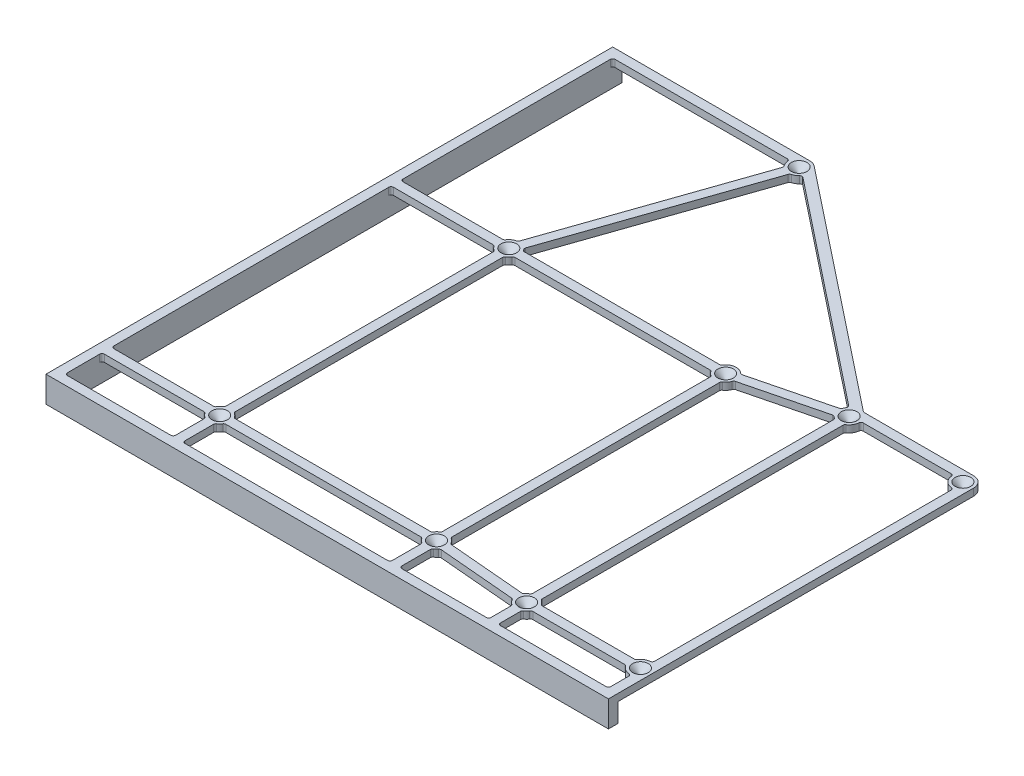
SolidWorks part; units mm, degrees
ref_plane "Front Plane" through (0, 0, 0) normal (0, 0, 1) x (1, 0, 0)
ref_plane "Top Plane" through (0, 0, 0) normal (0, 1, 0) x (1, 0, 0)
ref_plane "Right Plane" through (0, 0, 0) normal (1, 0, 0) x (0, 0, -1)
sketch "Sketch1" plane through (0, 0, 0) normal (0, 1, 0) x (1, 0, 0)
  line L0 (0, 0) -> (0, 15.62)
  line L1 (0, 234.9689) -> (-4, 234.9689)
  line L2 (-4, 234.9689) -> (-4, -4)
  line L3 (-4, -4) -> (233.18, -4)
  line L4 (233.18, -4) -> (233.18, 0)
  line L5 (229.18, 0) -> (182.68, 0)
  line L6 (180.68, 150) -> (228.68, 150) construction
  line L7 (47.62, 139.54) -> (139.06, 139.54) construction
  line L8 (47.62, 139.54) -> (47.62, 17.62) construction
  line L9 (47.62, 17.62) -> (139.06, 17.62) construction
  line L10 (139.06, 139.54) -> (139.06, 17.62) construction
  line L11 (146.68, 10) -> (40, 10) construction
  line L12 (146.68, 10) -> (146.68, 147.16) construction
  line L13 (146.68, 147.16) -> (40, 147.16) construction
  line L14 (40, 10) -> (40, 147.16) construction
  line L15 (180.68, 150) -> (180.68, 14) construction
  line L16 (180.68, 14) -> (228.68, 14) construction
  line L17 (228.68, 150) -> (228.68, 14) construction
  line L18 (232.68, 10) -> (176.68, 10) construction
  line L19 (232.68, 10) -> (232.68, 154) construction
  line L20 (232.68, 154) -> (176.68, 154) construction
  line L21 (176.68, 10) -> (176.68, 154) construction
  line L22 (229.18, 14) -> (233.18, 14) construction
  line L23 (233.18, 0) -> (233.18, 150)
  line L24 (229.18, 9.5279) -> (229.18, 0)
  line L25 (229.18, 18.4721) -> (229.18, 145.5279)
  line L26 (0, 234.9689) -> (79.1338, 234.9689)
  line L27 (228.68, 154.5) -> (182.2468, 154.5)
  line L28 (182.2468, 154.5) -> (81.9286, 233.9957)
  line L29 (178.68, 145.9689) -> (178.68, 18.0311)
  line L30 (185.1521, 150.5) -> (224.2079, 150.5)
  line L31 (184.7111, 16) -> (224.6489, 16)
  line L32 (184.7111, 12) -> (224.6489, 12)
  line L33 (224.6489, 16) -> (224.6489, 12) construction
  line L34 (224.6489, 16) -> (228.2321, 14.2222) construction
  line L35 (177.4855, 153.1694) -> (82.9494, 228.0832)
  line L36 (79.1338, 230.4689) -> (180.68, 150) construction
  line L37 (182.68, 145.9689) -> (182.68, 18.0311)
  line L38 (182.68, 9.9689) -> (182.68, 0)
  line L39 (178.68, 9.9689) -> (178.68, 0)
  line L40 (178.68, 18.0311) -> (182.68, 18.0311) construction
  line L41 (139.06, 17.62) -> (180.68, 14) construction
  line L42 (224.2079, 150.5) -> (224.2079, 154.5) construction
  line L43 (180.68, 150) -> (139.06, 139.54) construction
  line L44 (142.4821, 142.4622) -> (176.283, 150.9571)
  line L45 (141.06, 13.5889) -> (141.06, 0)
  line L46 (142.9027, 15.2782) -> (176.4907, 12.3568)
  line L47 (143.2493, 19.2632) -> (176.8373, 16.3418)
  line L48 (176.8373, 16.3418) -> (176.4907, 12.3568) construction
  line L49 (141.06, 21.6511) -> (141.06, 135.5089)
  line L50 (143.457, 138.5829) -> (177.2579, 147.0778)
  line L51 (176.283, 150.9571) -> (177.2579, 147.0778) construction
  line L52 (177.4855, 153.1694) -> (179.9698, 156.3044) construction
  line L53 (74.6616, 230.9689) -> (0, 230.9689)
  line L54 (74.6616, 230.9689) -> (74.6616, 234.9689) construction
  line L55 (45.62, 13.5889) -> (45.62, 0)
  line L56 (43.5889, 15.62) -> (0, 15.62)
  line L57 (51.6511, 15.62) -> (135.0289, 15.62)
  line L58 (49.62, 13.5889) -> (49.62, 0)
  line L59 (137.06, 13.5889) -> (137.06, 0)
  line L60 (51.6511, 19.62) -> (135.0289, 19.62)
  line L61 (137.06, 21.6511) -> (137.06, 135.5089)
  line L62 (75.924, 227.3149) -> (47.0503, 144.0038)
  line L63 (51.6511, 141.54) -> (135.0289, 141.54)
  line L64 (47.62, 139.54) -> (79.1338, 230.4689) construction
  line L65 (79.7034, 226.0051) -> (50.8298, 142.6939)
  line L66 (43.5889, 141.54) -> (0, 141.54)
  line L67 (43.5889, 137.54) -> (0, 137.54)
  line L68 (51.6511, 137.54) -> (135.0289, 137.54)
  line L69 (135.0289, 19.62) -> (135.0289, 15.62) construction
  line L70 (137.06, 13.5889) -> (141.06, 13.5889) construction
  line L71 (137.06, 21.6511) -> (141.06, 21.6511) construction
  line L72 (43.5889, 19.62) -> (0, 19.62)
  line L73 (45.62, 13.5889) -> (49.62, 13.5889) construction
  line L74 (45.62, 135.5089) -> (45.62, 21.6511)
  line L75 (49.62, 135.5089) -> (49.62, 21.6511)
  line L76 (135.0289, 137.54) -> (135.0289, 141.54) construction
  line L77 (47.0503, 144.0038) -> (50.8298, 142.6939) construction
  line L78 (0, 141.54) -> (0, 230.9689)
  line L79 (0, 19.62) -> (0, 137.54)
  line L80 (45.62, 0) -> (0, 0)
  line L81 (137.06, 0) -> (49.62, 0)
  line L82 (178.68, 0) -> (141.06, 0)
  circle A0 centre (47.62, 139.54) radius 7.62 construction
  circle A1 centre (139.06, 17.62) radius 7.62 construction
  circle A2 centre (47.62, 139.54) radius 0.5
  circle A3 centre (139.06, 139.54) radius 0.5
  circle A4 centre (139.06, 17.62) radius 0.5
  circle A5 centre (47.62, 17.62) radius 0.5
  circle A6 centre (180.68, 150) radius 4 construction
  circle A7 centre (228.68, 14) radius 4 construction
  circle A8 centre (180.68, 150) radius 0.5
  circle A9 centre (228.68, 150) radius 0.5
  circle A10 centre (228.68, 14) radius 0.5
  circle A11 centre (180.68, 14) radius 0.5
  arc A12 (229.18, 9.5279) -> (224.6489, 12) centre (228.68, 14) cw
  circle A13 centre (79.1338, 230.4689) radius 0.5
  arc A14 (233.18, 150) -> (228.68, 154.5) centre (228.68, 150) ccw
  arc A15 (79.1338, 234.9689) -> (81.9286, 233.9957) centre (79.1338, 230.4689) cw
  arc A16 (229.18, 18.4721) -> (224.6489, 16) centre (228.68, 14) ccw
  arc A17 (229.18, 145.5279) -> (224.2079, 150.5) centre (228.68, 150) cw
  arc A18 (185.1521, 150.5) -> (182.68, 145.9689) centre (180.68, 150) cw
  arc A19 (178.68, 9.9689) -> (176.4907, 12.3568) centre (180.68, 14) cw
  arc A20 (178.68, 18.0311) -> (176.8373, 16.3418) centre (180.68, 14) ccw
  arc A21 (182.68, 9.9689) -> (184.7111, 12) centre (180.68, 14) ccw
  arc A22 (184.7111, 16) -> (182.68, 18.0311) centre (180.68, 14) ccw
  arc A23 (177.4855, 153.1694) -> (176.283, 150.9571) centre (180.68, 150) ccw
  arc A24 (178.68, 145.9689) -> (177.2579, 147.0778) centre (180.68, 150) cw
  arc A25 (75.924, 227.3149) -> (74.6616, 230.9689) centre (79.1338, 230.4689) cw
  arc A26 (143.457, 138.5829) -> (141.06, 135.5089) centre (139.06, 139.54) cw
  arc A27 (143.2493, 19.2632) -> (141.06, 21.6511) centre (139.06, 17.62) ccw
  arc A28 (142.9027, 15.2782) -> (141.06, 13.5889) centre (139.06, 17.62) cw
  arc A29 (82.9494, 228.0832) -> (79.7034, 226.0051) centre (79.1338, 230.4689) cw
  arc A30 (137.06, 21.6511) -> (135.0289, 19.62) centre (139.06, 17.62) ccw
  arc A31 (137.06, 13.5889) -> (135.0289, 15.62) centre (139.06, 17.62) cw
  arc A32 (45.62, 13.5889) -> (43.5889, 15.62) centre (47.62, 17.62) cw
  arc A33 (43.5889, 19.62) -> (45.62, 21.6511) centre (47.62, 17.62) cw
  arc A34 (51.6511, 19.62) -> (49.62, 21.6511) centre (47.62, 17.62) ccw
  arc A35 (51.6511, 15.62) -> (49.62, 13.5889) centre (47.62, 17.62) cw
  arc A36 (137.06, 135.5089) -> (135.0289, 137.54) centre (139.06, 139.54) cw
  arc A37 (142.4821, 142.4622) -> (135.0289, 141.54) centre (139.06, 139.54) ccw
  arc A38 (51.6511, 137.54) -> (49.62, 135.5089) centre (47.62, 139.54) cw
  arc A39 (45.62, 135.5089) -> (43.5889, 137.54) centre (47.62, 139.54) cw
  arc A40 (43.5889, 141.54) -> (47.0503, 144.0038) centre (47.62, 139.54) cw
  arc A41 (50.8298, 142.6939) -> (51.6511, 141.54) centre (47.62, 139.54) cw
  point P101 (0, 0)
  dimension "D4" = 106.68
  dimension "D5" = 1
  dimension "D8" = 108.9
  dimension "D13" = 96.235
  dimension "D1" = 4
  dimension "D2" = 121.92
  dimension "D3" = 91.44
  dimension "D6" = 40
  dimension "D7" = 10
  dimension "D9" = 48
  dimension "D10" = 136
  dimension "D11" = 56
  dimension "D12" = 30
extrude "Boss-Extrude1" add sketch "Sketch1" along normal blind 3
sketch "Sketch2" plane through (0, 0, 0) normal (0, -1, 0) x (1, 0, 0)
  line L0 (-4, 4) -> (-4, -234.9689)
  line L1 (-4, -234.9689) -> (-4, 4) construction
  line L2 (-4, -234.9689) -> (0, -234.9689)
  line L3 (79.1338, -234.9689) -> (-4, -234.9689) construction
  line L4 (0, -234.9689) -> (0, 0)
  line L5 (0, 0) -> (233.18, 0)
  line L6 (233.18, 4) -> (233.18, -150) construction
  line L7 (233.18, 0) -> (233.18, 4)
  line L8 (233.18, 4) -> (-4, 4)
  point P13 (-4, -248.5482)
extrude "Boss-Extrude2" add sketch "Sketch2" along normal blind 8
chamfer "Chamfer1" distance 2.8 angle 45 9 edges at (47.62, 3, -17.12) (139.06, 3, -17.12) (180.68, 3, -13.5) (228.68, 3, -13.5) (228.68, 3, -149.5) (180.68, 3, -149.5) (139.06, 3, -139.04) (79.1338, 3, -229.9689) (47.62, 3, -139.04)
fillet "Fillet1" radius 1 68 edges at (182.2468, 1.5, -154.5) (176.8373, 1.5, -16.3418) (178.68, 1.5, -18.0311) (49.62, 1.5, 0) (0, -2.5, 0) (45.62, 1.5, 0) (45.62, 1.5, -13.5889) (43.5889, 1.5, -15.62) (43.5889, 1.5, -19.62) (45.62, 1.5, -21.6511) (49.62, 1.5, -21.6511) (51.6511, 1.5, -19.62) (49.62, 1.5, -13.5889) (51.6511, 1.5, -15.62) (0, 1.5, -15.62) (0, 1.5, -19.62) (0, 1.5, -137.54) (0, 1.5, -141.54) (43.5889, 1.5, -141.54) (47.0503, 1.5, -144.0038) (43.5889, 1.5, -137.54) (45.62, 1.5, -135.5089) (49.62, 1.5, -135.5089) (51.6511, 1.5, -137.54) (51.6511, 1.5, -141.54) (50.8298, 1.5, -142.6939) (142.4821, 1.5, -142.4622) (135.0289, 1.5, -141.54) (143.457, 1.5, -138.5829) (141.06, 1.5, -135.5089) (137.06, 1.5, -135.5089) (135.0289, 1.5, -137.54) (135.0289, 1.5, -19.62) (137.06, 1.5, -21.6511) (137.06, 1.5, 0) (141.06, 1.5, 0) (141.06, 1.5, -21.6511) (143.2493, 1.5, -19.2632) (182.68, 1.5, -18.0311) (184.7111, 1.5, -16) (182.68, 1.5, 0) (178.68, 1.5, 0) (229.18, 1.5, 0) (137.06, 1.5, -13.5889) (135.0289, 1.5, -15.62) (141.06, 1.5, -13.5889) (142.9027, 1.5, -15.2782) (182.68, 1.5, -9.9689) (184.7111, 1.5, -12) (176.4907, 1.5, -12.3568) (178.68, 1.5, -9.9689) (229.18, 1.5, -9.5279) (224.6489, 1.5, -12) (224.6489, 1.5, -16) (229.18, 1.5, -18.4721) (229.18, 1.5, -145.5279) (224.2079, 1.5, -150.5) (182.68, 1.5, -145.9689) (185.1521, 1.5, -150.5) (178.68, 1.5, -145.9689) (177.2579, 1.5, -147.0778) (176.283, 1.5, -150.9571) (177.4855, 1.5, -153.1694) (74.6616, 1.5, -230.9689) (75.924, 1.5, -227.3149) (79.7034, 1.5, -226.0051) (82.9494, 1.5, -228.0832) (0, 1.5, -230.9689)
